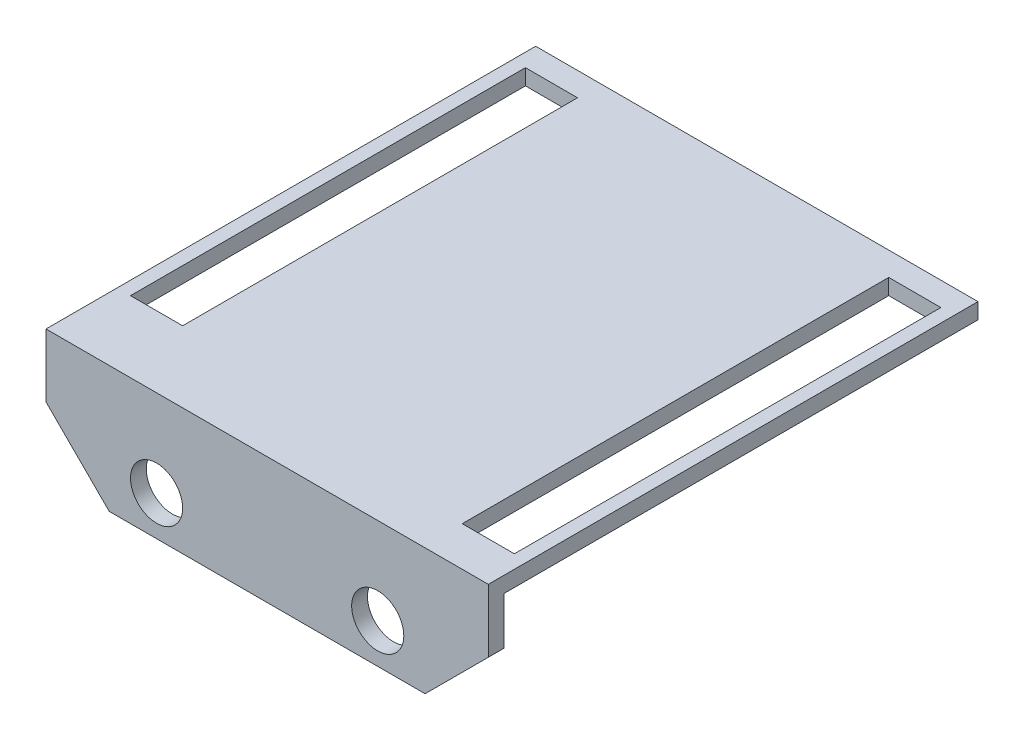
SolidWorks part; units mm, degrees
ref_plane "Front Plane" through (0, 0, 0) normal (0, 0, 1) x (1, 0, 0)
ref_plane "Top Plane" through (0, 0, 0) normal (0, 1, 0) x (1, 0, 0)
ref_plane "Right Plane" through (0, 0, 0) normal (1, 0, 0) x (0, 0, -1)
sketch "Sketch1" plane through (0, 0, 0) normal (0, 0, 1) x (1, 0, 0)
  line L1 (-14, -4) -> (14, -4)
  line L2 (-14, -4) -> (-14, 4)
  line L3 (-14, 4) -> (14, 4)
  line L4 (14, -4) -> (14, 4)
  line L5 (-14, -4) -> (14, 4) construction
  line L6 (-14, 4) -> (14, -4) construction
  point P0 (0, 0)
  dimension "D1" = 28
  dimension "D2" = 8
extrude "Boss-Extrude1" add sketch "Sketch1" along normal blind 1
sketch "Sketch2" plane through (0, 0, 0) normal (0, 0, -1) x (-1, 0, 0)
  line L0 (14, 4) -> (14, -4) construction
  line L1 (-14, 4) -> (14, 4)
  line L2 (-14, 4) -> (-14, 3)
  line L3 (-14, 3) -> (14, 3)
  line L4 (14, 4) -> (14, 3)
  dimension "D1" = 1
extrude "Boss-Extrude2" add sketch "Sketch2" along normal blind 30
sketch "Sketch3" plane through (0, 0, 1) normal (0, 0, 1) x (1, 0, 0)
  line L0 (-14, -4) -> (14, -4) construction
  line L1 (14, -4) -> (14, 4) construction
  line L2 (-14, 4) -> (-14, -4) construction
  circle A0 centre (-7, -1.5) radius 1.65
  circle A1 centre (7, -1.5) radius 1.65
  dimension "D1" = 3.3
  dimension "D2" = 3.3
  dimension "D3" = 2.5
  dimension "D4" = 7
  dimension "D5" = 7
  dimension "D6" = 2.5
extrude "Cut-Extrude1" cut sketch "Sketch3" against normal blind 1
sketch "Sketch4" plane through (0, 4, 0) normal (0, 1, 0) x (1, 0, 0)
  line L0 (-14, 30) -> (14, 30) construction
  line L1 (-14, -1) -> (-14, 30) construction
  line L3 (13.15, 28.5) -> (9.85, 28.5)
  line L4 (13.15, 28.5) -> (13.15, 1.5)
  line L5 (13.15, 1.5) -> (9.85, 1.5)
  line L6 (9.85, 28.5) -> (9.85, 1.5)
  line L7 (-13.15, 28.5) -> (-9.85, 28.5)
  line L8 (-13.15, 28.5) -> (-13.15, 3.5)
  line L9 (-13.15, 3.5) -> (-9.85, 3.5)
  line L10 (-9.85, 28.5) -> (-9.85, 3.5)
  point P16 (11.5, 28.5)
  point P17 (-11.5, 28.5)
  dimension "D7" = 3.3
  dimension "D8" = 3.3
  dimension "D9" = 23
  dimension "D10" = 2.5
  dimension "D11" = 25
  dimension "D12" = 27
  dimension "D13" = 1.5
  dimension "D14" = 1.5
chamfer "Chamfer1" distance 4 angle 45 2 edges at (14, -4, 0.5) (-14, -4, 0.5)
extrude "Cut-Extrude2" cut sketch "Sketch4" against normal blind 10
